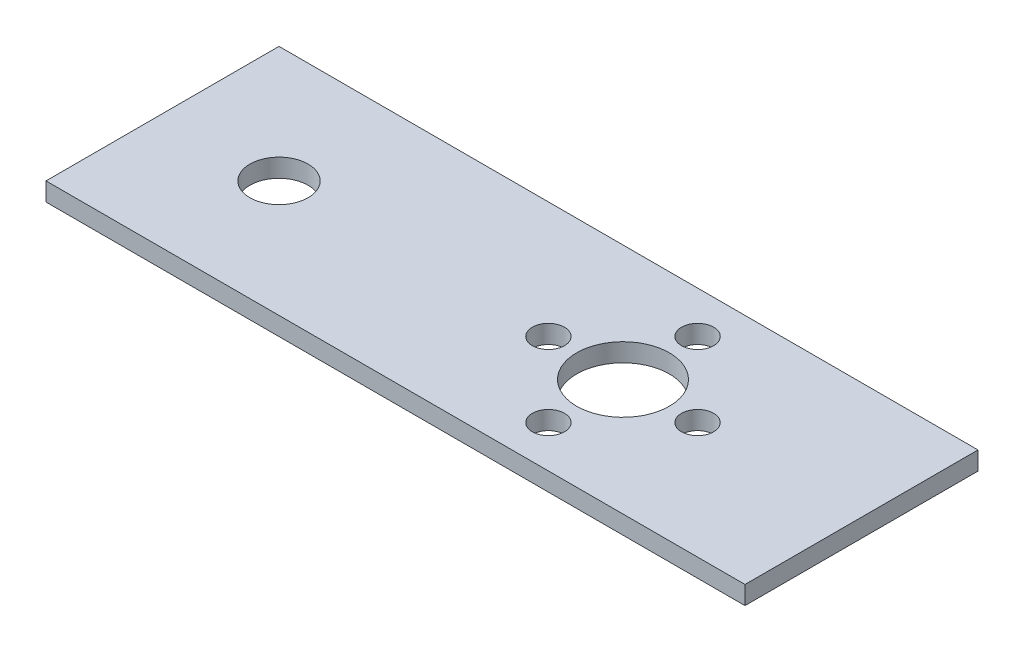
SolidWorks part; units mm, degrees
material "AISI 1020"
ref_plane "Front Plane" through (0, 0, 0) normal (0, 0, 1) x (1, 0, 0)
ref_plane "Top Plane" through (0, 0, 0) normal (0, 1, 0) x (1, 0, 0)
ref_plane "Right Plane" through (0, 0, 0) normal (1, 0, 0) x (0, 0, -1)
sketch "Sketch1" plane through (0, 0, 0) normal (0, 1, 0) x (1, 0, 0)
  line L0 (-37.8, 0) -> (12.4, 0) construction
  line L1 (-37.8, -12.7) -> (38.4, -12.7)
  line L2 (-37.8, -12.7) -> (-37.8, 12.7)
  line L3 (-37.8, 12.7) -> (38.4, 12.7)
  line L4 (38.4, -12.7) -> (38.4, 12.7)
  line L5 (0, 0) -> (14.1201, 4.748) construction
  line L6 (0, 0) -> (14.1201, -4.748) construction
  line L7 (12.4, 0) -> (12.4, 8.13) construction
  circle A0 centre (12.4, 0) radius 5.05
  circle A1 centre (12.4, 8.13) radius 1.75
  circle A2 centre (20.53, 0) radius 1.75
  circle A3 centre (12.4, -8.13) radius 1.75
  circle A4 centre (4.27, 0) radius 1.75
  circle A5 centre (-25.1, 0) radius 3.175
  point P0 (0, 0)
  dimension "D3" = 8.13
  dimension "D4" = 3.5
  dimension "D6" = 10.1
  dimension "D8" = 6.35
  dimension "D1" = 25.4
  dimension "D2" = 50.2
  dimension "3in" = 76.2
  dimension "D7" = 12.7
  dimension "D5" = 4
extrude "Boss-Extrude1" add sketch "Sketch1" along normal blind 2
